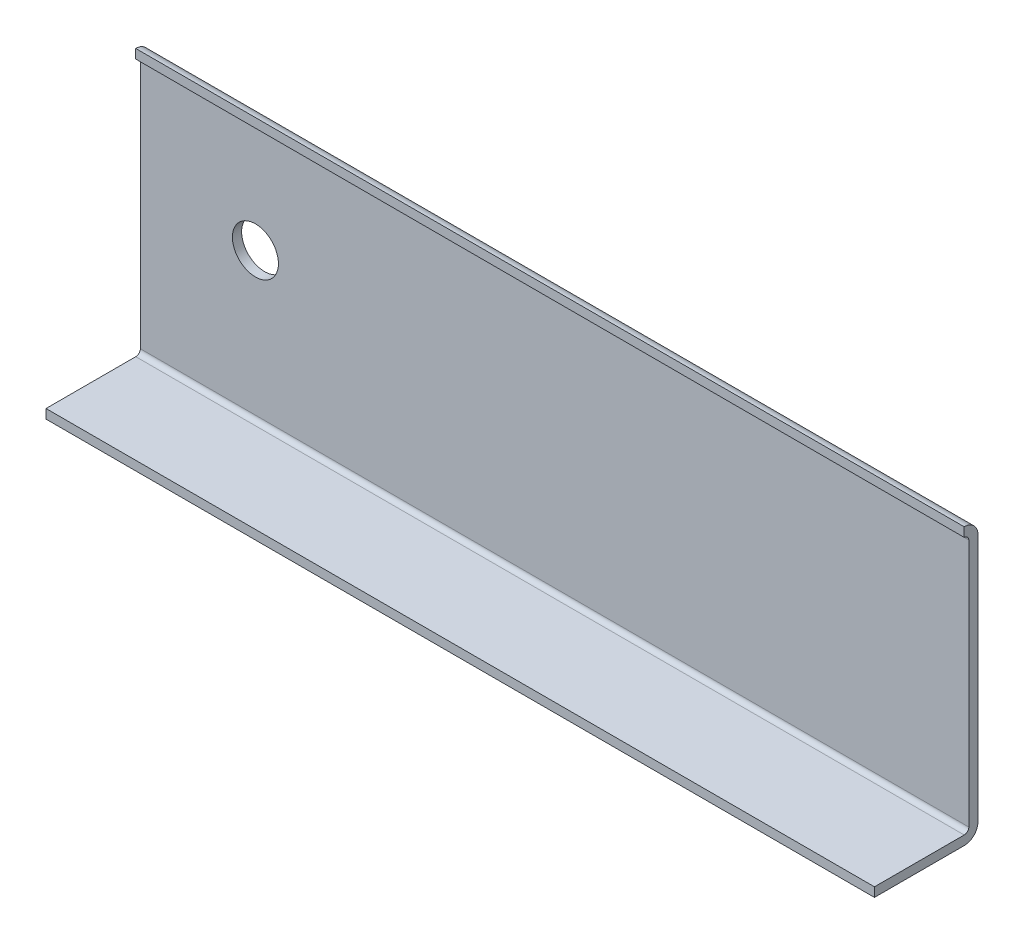
SolidWorks part; units mm, degrees
ref_plane "Спереди" through (0, 0, 0) normal (0, 0, 1) x (1, 0, 0)
ref_plane "Сверху" through (0, 0, 0) normal (0, 1, 0) x (1, 0, 0)
ref_plane "Справа" through (0, 0, 0) normal (1, 0, 0) x (0, 0, -1)
sketch "Эскиз1" plane through (0, 0, 0) normal (1, 0, 0) x (0, 0, -1)
  line L1 (1, 0) -> (35, 0)
  line L2 (0, 1) -> (0, 55)
  line L3 (1, 56) -> (35, 56)
  line L4 (36, 1) -> (36, 55)
  arc A4 (1, 0) -> (0, 1) centre (1, 1) cw
  arc A5 (35, 0) -> (36, 1) centre (35, 1) ccw
  arc A6 (36, 55) -> (35, 56) centre (35, 55) ccw
  arc A7 (0, 55) -> (1, 56) centre (1, 55) cw
  point P3 (0, 0)
  point P8 (0, 0)
  dimension "D1" = 1
extrude "Вытянуть-Тонкостенный1" add sketch "Эскиз1" along normal blind 180 thin
sketch "Эскиз2" plane through (0, -2, 0) normal (0, -1, 0) x (1, 0, 0)
  line L0 (180, -1) -> (180, -35) construction
  line L1 (0, 2) -> (180, 2)
  line L2 (0, 2) -> (0, -15.5)
  line L3 (0, -15.5) -> (180, -15.5)
  line L4 (180, 2) -> (180, -15.5)
  line L5 (0, -1) -> (0, -35) construction
  point P7 (0, -11.1209)
extrude "Вырез-Вытянуть1" cut sketch "Эскиз2" against normal blind 45
sketch "Эскиз3" plane through (0, 58, 0) normal (0, 1, 0) x (1, 0, 0)
  line L1 (0, 35) -> (180, 35)
  line L2 (0, 35) -> (0, -2)
  line L3 (0, -2) -> (180, -2)
  line L4 (180, 35) -> (180, -2)
  point P4 (240, 35)
extrude "Вырез-Вытянуть2" cut sketch "Эскиз3" against normal blind 25
sketch "Эскиз4" plane through (0, 0, -38) normal (0, 0, -1) x (-1, 0, 0)
  circle A0 centre (-25, 32) radius 5
  point P2 (0, 0)
  point P3 (0, 0)
  point P4 (0, 0)
extrude "Вырез-Вытянуть3" cut sketch "Эскиз4" against normal blind 10
